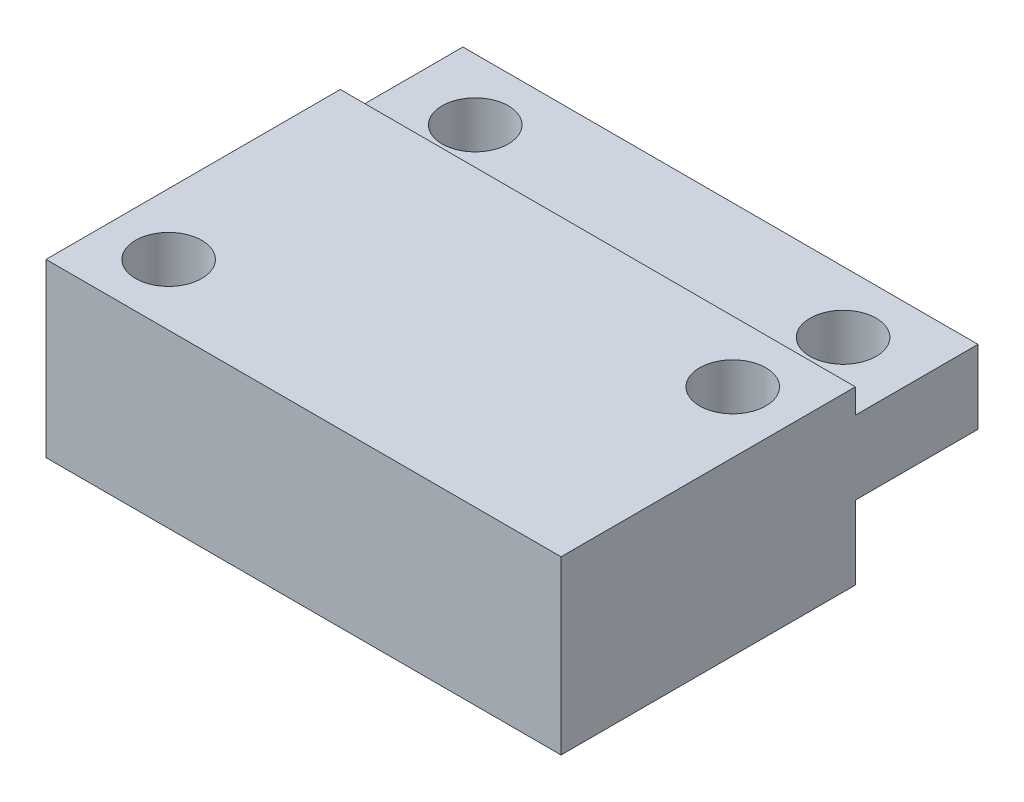
SolidWorks part; units mm, degrees
material "AISI 316 Stainless Steel Sheet (SS)"
ref_plane "Front Plane" through (0, 0, 0) normal (0, 0, 1) x (1, 0, 0)
ref_plane "Top Plane" through (0, 0, 0) normal (0, 1, 0) x (1, 0, 0)
ref_plane "Right Plane" through (0, 0, 0) normal (1, 0, 0) x (0, 0, -1)
sketch "Sketch1" plane through (0, 0, 0) normal (0, 1, 0) x (1, 0, 0)
  line L1 (-10.5, 8.5) -> (10.5, 8.5)
  line L2 (-10.5, 8.5) -> (-10.5, -8.5)
  line L3 (-10.5, -8.5) -> (10.5, -8.5)
  line L4 (10.5, 8.5) -> (10.5, -8.5)
  point P4 (0, -8.5)
  point P6 (-10.5, 0)
  dimension "D1" = 21
  dimension "D2" = 17
extrude "Boss-Extrude1" add sketch "Sketch1" along normal blind 7
sketch "Sketch2" plane through (0, 7, 0) normal (0, 1, 0) x (1, 0, 0)
  line L0 (10.5, -8.5) -> (10.5, 8.5) construction
  line L1 (-10.5, 8.5) -> (10.5, 8.5)
  line L2 (-10.5, 8.5) -> (-10.5, 3.5)
  line L3 (-10.5, 3.5) -> (10.5, 3.5)
  line L4 (10.5, 8.5) -> (10.5, 3.5)
  dimension "D1" = 5
extrude "Cut-Extrude1" cut sketch "Sketch2" against normal blind 1
hole_wizard "M2.5 Clearance Hole1" positions "Sketch3" profile "Sketch4" hole size "M2.5" standard "ISO" end condition through all
sketch "Sketch3" plane through (0, 7, 0) normal (0, 1, 0) x (1, 0, 0)
  line L0 (-10.5, -8.5) -> (10.5, -8.5) construction
  line L1 (-10.5, 3.5) -> (-10.5, -8.5) construction
  line L2 (10.5, -8.5) -> (10.5, 3.5) construction
  point P0 (-8, -6)
  point P2 (8, 1)
  dimension "D1" = 2.5
  dimension "D2" = 2.5
  dimension "D3" = 2.5
  dimension "D4" = 7
sketch "Sketch4" plane through (-8, 7, 6) normal (1, 0, 0) x (0, 0, 1)
  line L0 (0, 0) -> (0, 7)
  line L1 (0, 7) -> (1.35, 7)
  line L2 (1.35, 7) -> (1.35, 0)
  line L5 (1.35, 0) -> (0, 0)
  line L11 (0, -6.35) -> (0, 107.95) construction
  dimension "Thru Hole Dia." = 2.7
  dimension "Thru Hole Depth" = 7
sketch "Sketch5" plane through (0, 0, 0) normal (0, -1, 0) x (1, 0, 0)
  line L0 (-10.5, -8.5) -> (-10.5, 8.5) construction
  line L1 (10.5, -8.5) -> (-10.5, -8.5)
  line L2 (10.5, -8.5) -> (10.5, -3.5)
  line L3 (10.5, -3.5) -> (-10.5, -3.5)
  line L4 (-10.5, -8.5) -> (-10.5, -3.5)
  line L5 (-10.5, -3.5) -> (10.5, -3.5) construction
  line L6 (-10.5, -3.5) -> (10.5, -3.5)
  line M5 (-10.5, 8.5) -> (-10.5, -8.5)
  line M6 (-10.5, -8.5) -> (10.5, -8.5)
  line M7 (10.5, -8.5) -> (10.5, 8.5)
extrude "Cut-Extrude2" cut sketch "Sketch5" against normal blind 3 contours L3 M7 M5 M6
hole_wizard "M2.5 Clearance Hole2" positions "Sketch6" profile "Sketch7" hole size "M2.5" standard "ISO" end condition through all
sketch "Sketch6" plane through (0, 3, 0) normal (0, -1, 0) x (-1, 0, 0)
  line L0 (-10.5, 8.5) -> (-10.5, 3.5) construction
  line L1 (-10.5, 8.5) -> (-10.5, 3.5)
  line L3 (10.5, 8.5) -> (-10.5, 8.5) construction
  line L4 (10.5, 3.5) -> (10.5, 8.5) construction
  point P0 (-7.5, 6)
  point P2 (7.5, 6)
  dimension "D1" = 3
  dimension "D2" = 3
  dimension "D3" = 2.5
sketch "Sketch7" plane through (7.5, 3, -6) normal (1, 0, 0) x (0, 0, -1)
  line L0 (0, 0) -> (0, 4)
  line L1 (0, 4) -> (1.35, 4)
  line L2 (1.35, 4) -> (1.35, 0)
  line L5 (1.35, 0) -> (0, 0)
  line L11 (0, -6.35) -> (0, 107.95) construction
  dimension "Thru Hole Dia." = 2.7
  dimension "Thru Hole Depth" = 4
